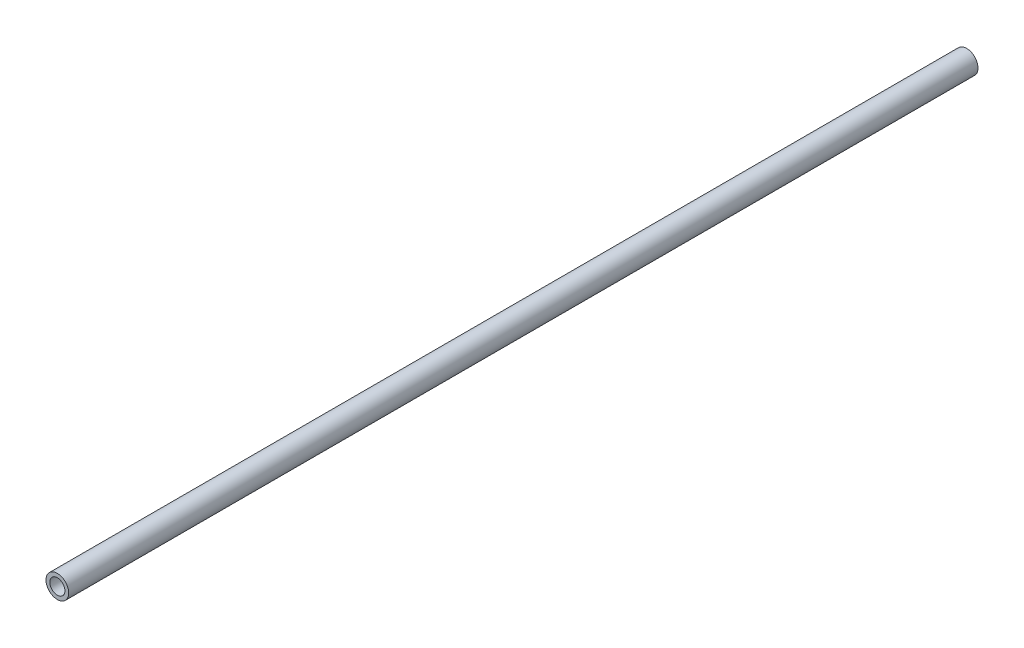
SolidWorks part; units mm, degrees
material "PVC Rigid"
ref_plane "Front Plane" through (0, 0, 0) normal (0, 0, 1) x (1, 0, 0)
ref_plane "Top Plane" through (0, 0, 0) normal (0, 1, 0) x (1, 0, 0)
ref_plane "Right Plane" through (0, 0, 0) normal (1, 0, 0) x (0, 0, -1)
sketch "Sketch2" plane through (0, 0, 0) normal (0, 0, 1) x (1, 0, 0)
  circle A0 centre (0, 0) radius 7.62
  circle A2 centre (0, 0) radius 5.08
  dimension "D1" = 15.24
  dimension "D2" = 10.16
extrude "Boss-Extrude1" add sketch "Sketch2" along normal blind 609.6
